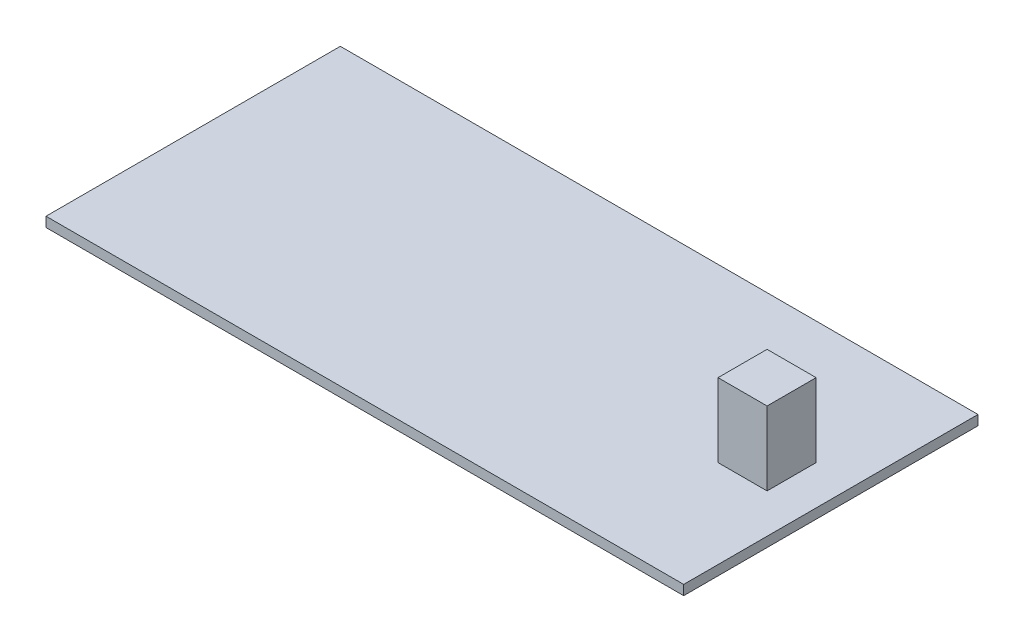
SolidWorks part; units mm, degrees
ref_plane "Front Plane" through (0, 0, 0) normal (0, 0, 1) x (1, 0, 0)
ref_plane "Top Plane" through (0, 0, 0) normal (0, 1, 0) x (1, 0, 0)
ref_plane "Right Plane" through (0, 0, 0) normal (1, 0, 0) x (0, 0, -1)
sketch "Sketch1" plane through (0, 0, 0) normal (0, 1, 0) x (1, 0, 0)
  line L0 (0, 0) -> (435, 0) construction
  line L1 (-150, 150) -> (150, 150)
  line L2 (-150, 150) -> (-150, -150)
  line L3 (-150, -150) -> (150, -150)
  line L4 (150, 150) -> (150, -150)
  line L5 (-150, 150) -> (150, -150) construction
  line L6 (-150, -150) -> (150, 150) construction
  line L7 (150, 150) -> (500, 150)
  line L8 (150, 150) -> (150, -150)
  line L9 (150, -150) -> (500, -150)
  line L10 (500, 150) -> (500, -150)
  point P0 (0, 0)
  point P10 (0, 0)
  dimension "D1" = 300
  dimension "D2" = 435
  dimension "D3" = 350
extrude "Boss-Extrude1" add sketch "Sketch1" against normal mid plane 10 contours L4 L1 L2 L3 | L10 L7 L4 L9
sketch "Sketch2" plane through (0, 5, 0) normal (0, 1, 0) x (1, 0, 0)
  line L1 (410, -25) -> (460, -25)
  line L2 (410, -25) -> (410, 25)
  line L3 (410, 25) -> (460, 25)
  line L4 (460, -25) -> (460, 25)
  line L5 (410, -25) -> (460, 25) construction
  line L6 (410, 25) -> (460, -25) construction
  point P0 (435, 0)
  point P5 (0, 0)
  dimension "D1" = 50
  dimension "D2" = 50
  dimension "D3" = 435
extrude "Boss-Extrude2" add sketch "Sketch2" along normal blind 75
